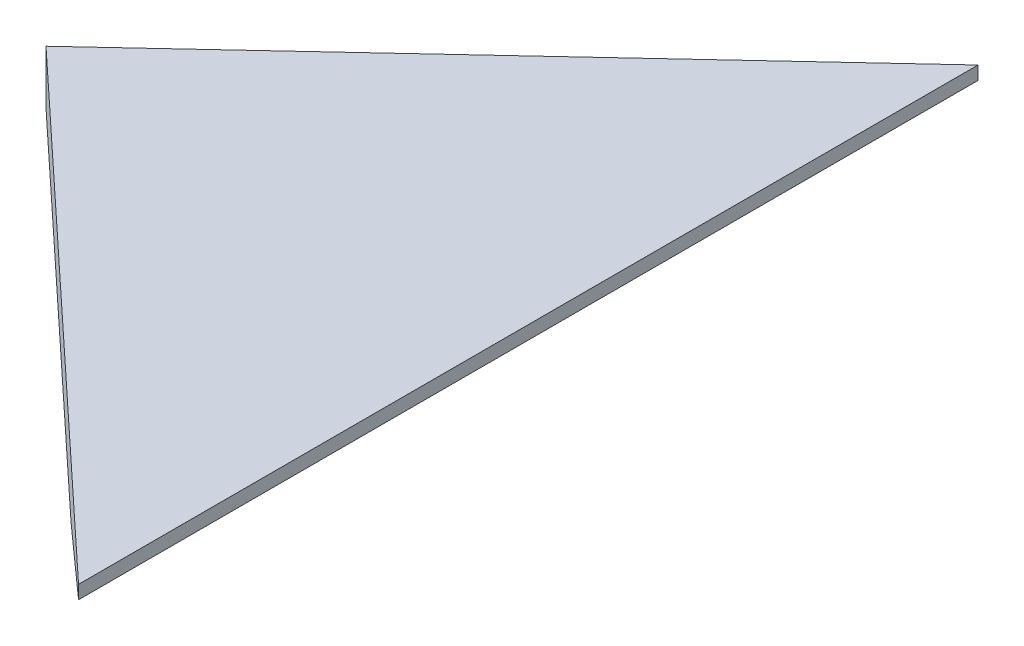
SolidWorks part; units mm, degrees
material "Pine"
ref_plane "Front Plane" through (0, 0, 0) normal (0, 0, 1) x (1, 0, 0)
ref_plane "Top Plane" through (0, 0, 0) normal (0, 1, 0) x (1, 0, 0)
ref_plane "Right Plane" through (0, 0, 0) normal (1, 0, 0) x (0, 0, -1)
sketch "Sketch1" plane through (0, 0, 0) normal (0, 0, 1) x (1, 0, 0)
  line L0 (0, 0) -> (0, 12.7)
  line L1 (0, 12.7) -> (114.3, 12.7)
  line L2 (114.3, 12.7) -> (114.3, 9.525)
  line L3 (114.3, 9.525) -> (88.1303, 0)
  line L4 (88.1303, 0) -> (0, 0)
  dimension "D1" = 114.3
  dimension "D2" = 3.175
  dimension "D3" = 12.7
  dimension "D4" = 20
extrude "Boss-Extrude1" add sketch "Sketch1" along normal mid plane 304.8
sketch "Sketch2" plane through (0, 0, 0) normal (0, 1, 0) x (1, 0, 0)
  line L0 (0, 0) -> (155.2643, -144.7863)
  line L1 (155.2643, -144.7863) -> (155.2643, 144.7863)
  line L2 (155.2643, 144.7863) -> (0, 0)
  dimension "D1" = 86
extrude "Cut-Extrude2" cut sketch "Sketch2" along normal through all flip side to cut
